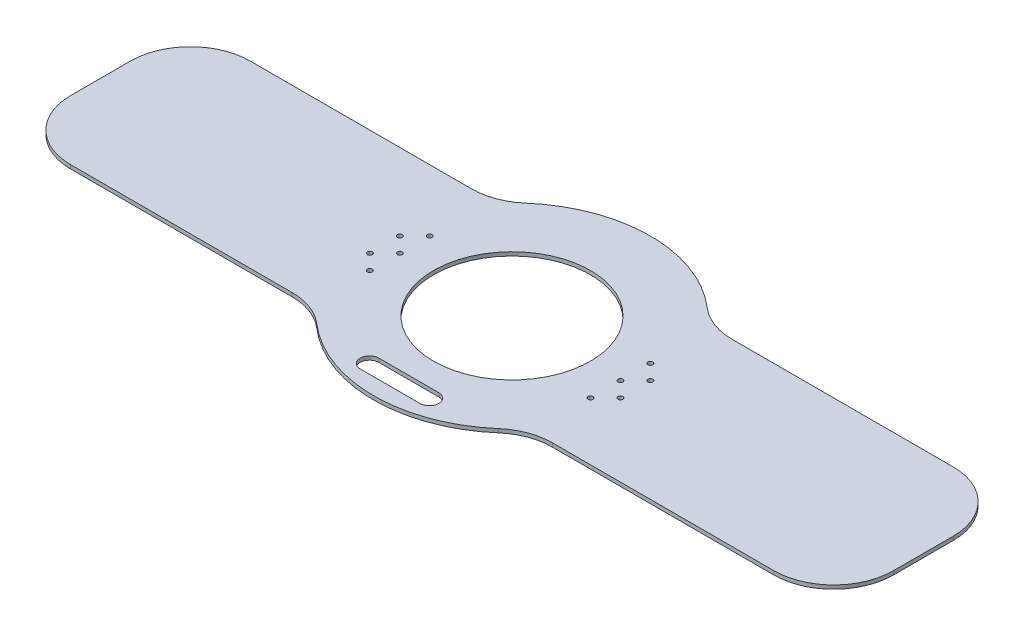
SolidWorks part; units mm, degrees
ref_plane "Front Plane" through (0, 0, 0) normal (0, 0, 1) x (1, 0, 0)
ref_plane "Top Plane" through (0, 0, 0) normal (0, 1, 0) x (1, 0, 0)
ref_plane "Right Plane" through (0, 0, 0) normal (1, 0, 0) x (0, 0, -1)
sketch "Sketch1" plane through (0, 0, 0) normal (0, 1, 0) x (1, 0, 0)
  line L0 (-110.3969, 76.2) -> (-298.45, 76.2)
  line L1 (298.45, 76.2) -> (110.3969, 76.2)
  line L2 (349.25, 25.4) -> (349.25, -25.4)
  line L3 (298.45, -76.2) -> (110.3969, -76.2)
  line L4 (-349.25, 25.4) -> (-349.25, -25.4)
  line L7 (-110.3969, -76.2) -> (-298.45, -76.2)
  circle A0 centre (0, 0) radius 66.675
  arc A1 (77.0695, 88.6604) -> (-77.0695, 88.6604) centre (0, 0) ccw
  arc A2 (-110.3969, 76.2) -> (-77.0695, 88.6604) centre (-110.3969, 127) ccw
  arc A3 (110.3969, 76.2) -> (77.0695, 88.6604) centre (110.3969, 127) cw
  arc A4 (298.45, 76.2) -> (349.25, 25.4) centre (298.45, 25.4) cw
  arc A5 (349.25, -25.4) -> (298.45, -76.2) centre (298.45, -25.4) cw
  arc A6 (-298.45, -76.2) -> (-349.25, -25.4) centre (-298.45, -25.4) cw
  arc A7 (-298.45, 76.2) -> (-349.25, 25.4) centre (-298.45, 25.4) ccw
  arc A8 (110.3969, -76.2) -> (77.0695, -88.6604) centre (110.3969, -127) ccw
  arc A9 (-110.3969, -76.2) -> (-77.0695, -88.6604) centre (-110.3969, -127) cw
  arc A13 (-77.0695, -88.6604) -> (77.0695, -88.6604) centre (0, 0) ccw
  point P4 (0, 0)
  point P13 (-89.4088, 76.2)
  point P16 (89.4088, 76.2)
  dimension "D1" = 133.35
  dimension "D2" = 234.95
  dimension "D5" = 50.8
  dimension "D6" = 152.4
  dimension "D7" = 76.2
  dimension "D8" = 50.8
  dimension "D4" = 349.25
  dimension "D3" = 349.25
extrude "Boss-Extrude1" add sketch "Sketch1" along normal blind 3.175
sketch "Sketch7" plane through (0, 3.175, 0) normal (0, 1, 0) x (1, 0, 0)
  line L0 (-25.4, -95.4996) -> (25.4, -95.4996) construction
  line L1 (-25.4, -87.5621) -> (25.4, -87.5621)
  line L2 (-25.4, -103.4371) -> (25.4, -103.4371)
  arc A0 (-25.4, -87.5621) -> (-25.4, -103.4371) centre (-25.4, -95.4996) ccw
  arc A1 (25.4, -103.4371) -> (25.4, -87.5621) centre (25.4, -95.4996) ccw
  point P2 (0, -95.4996)
  dimension "D1" = 15.875
  dimension "D2" = 95.4996
  dimension "D3" = 50.8
extrude "Cut-Extrude4" cut sketch "Sketch7" against normal up to surface (3.175 mm away) up to face at (0, 0, 66.675)
sketch "Sketch10" plane through (0, 3.175, 0) normal (0, 1, 0) x (1, 0, 0)
  line L1 (0, 0) -> (0, 34.774) construction
  line L2 (25.4, -87.5621) -> (-25.4, -87.5621) construction
  circle A0 centre (-93.6244, -26.9875) radius 2.0955
  circle A1 centre (-106.3244, -14.2875) radius 2.0955
  circle A2 centre (-93.6244, -1.5875) radius 2.0955
  circle A3 centre (-106.3244, 11.1125) radius 2.0955
  circle A4 centre (-93.6244, 23.8125) radius 2.0955
  circle A5 centre (93.6244, -26.9875) radius 2.0955
  circle A6 centre (106.3244, -14.2875) radius 2.0955
  circle A7 centre (93.6244, -1.5875) radius 2.0955
  circle A8 centre (106.3244, 11.1125) radius 2.0955
  circle A9 centre (93.6244, 23.8125) radius 2.0955
  dimension "D1" = 4.191
  dimension "D2" = 68.2244
  dimension "D3" = 80.9244
  dimension "D4" = 119.0244
  dimension "D5" = 60.5746
  dimension "D6" = 73.2746
  dimension "D7" = 85.9746
  dimension "D8" = 98.6746
  dimension "D9" = 111.3746
extrude "Cut-Extrude7" cut sketch "Sketch10" against normal through all
